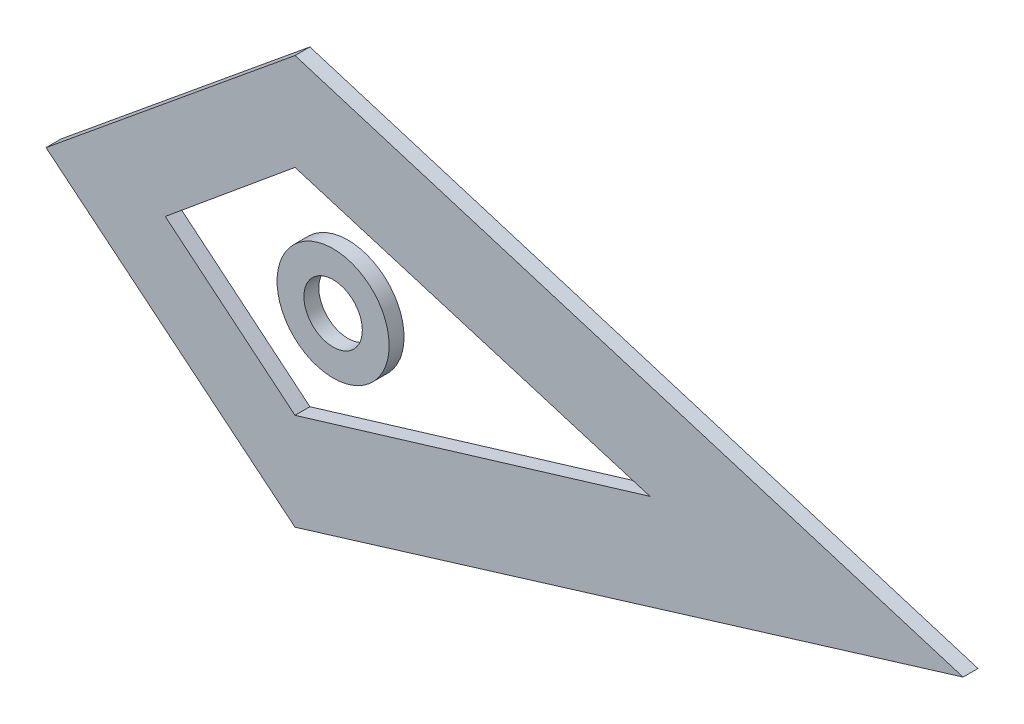
SolidWorks part; units mm, degrees
ref_plane "Front Plane" through (0, 0, 0) normal (0, 0, 1) x (1, 0, 0)
ref_plane "Top Plane" through (0, 0, 0) normal (0, 1, 0) x (1, 0, 0)
ref_plane "Right Plane" through (0, 0, 0) normal (1, 0, 0) x (0, 0, -1)
sketch "Sketch1" plane through (0, 0, 0) normal (0, 0, 1) x (1, 0, 0)
  line L0 (21.3094, 98.413) -> (363.976, 98.413) construction
  line L1 (-9.5465, 0) -> (-4.9745, 0) construction
  line L2 (-6.4918, 0) -> (-6.4918, 18.288) construction
  line L3 (-6.4918, 0) -> (-6.4918, -18.288) construction
  line L4 (9.5465, 0) -> (53.9965, 0) construction
  line L5 (-6.4918, 18.288) -> (53.9965, 0)
  line L6 (53.9965, 0) -> (-6.4918, -18.288)
  line L7 (-9.5465, 0) -> (-28.5965, 0) construction
  line L8 (-28.5965, 0) -> (-6.4918, 18.288)
  line L9 (-28.5965, 0) -> (-6.4918, -18.288)
  line L10 (-28.5965, 0) -> (-48.9165, 0) construction
  line L11 (-6.4918, 18.288) -> (-6.4918, 34.798) construction
  line L12 (-6.4918, -18.288) -> (-6.4918, -34.798) construction
  line L13 (53.9965, 0) -> (107.3365, 0) construction
  line L14 (-6.4918, 34.798) -> (107.3365, 0)
  line L15 (107.3365, 0) -> (-6.4918, -34.798)
  line L16 (-6.4918, -34.798) -> (-48.9165, 0)
  line L17 (-48.9165, 0) -> (-6.4918, 34.798)
  circle A0 centre (0, 0) radius 4.9745
  circle A1 centre (0, 0) radius 9.5465
extrude "Boss-Extrude1" add sketch "Sketch1" along normal blind 2.54 contours L17 L16 L15 L14 L9 L8 L5 L6 | A1 A0
